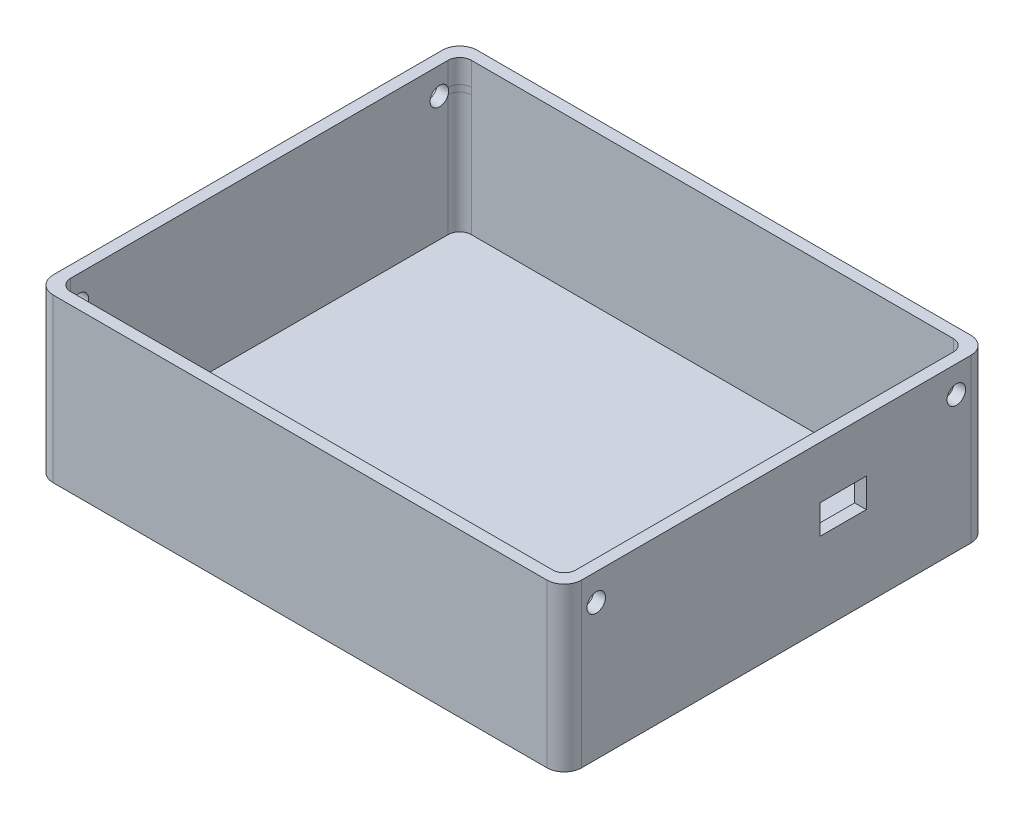
SolidWorks part; units mm, degrees
ref_plane "前视基准面" through (0, 0, 0) normal (0, 0, 1) x (1, 0, 0)
ref_plane "上视基准面" through (0, 0, 0) normal (0, 1, 0) x (1, 0, 0)
ref_plane "右视基准面" through (0, 0, 0) normal (1, 0, 0) x (0, 0, -1)
sketch "草图1" plane through (0, 0, 0) normal (0, 1, 0) x (1, 0, 0)
  line L1 (-45.5, 36.5) -> (45.5, 36.5)
  line L2 (-45.5, 36.5) -> (-45.5, -36.5)
  line L3 (-45.5, -36.5) -> (45.5, -36.5)
  line L4 (45.5, 36.5) -> (45.5, -36.5)
  line L5 (-45.5, 36.5) -> (45.5, -36.5) construction
  line L6 (-45.5, -36.5) -> (45.5, 36.5) construction
  point P0 (0, 0)
  dimension "D1" = 91
  dimension "D2" = 73
extrude "凸台-拉伸1" add sketch "草图1" along normal blind 28
sketch "草图2" plane through (0, 28, 0) normal (0, 1, 0) x (1, 0, 0)
  line L1 (-43.5, 34.5) -> (43.5, 34.5)
  line L2 (-43.5, 34.5) -> (-43.5, -34.5)
  line L3 (-43.5, -34.5) -> (43.5, -34.5)
  line L4 (43.5, 34.5) -> (43.5, -34.5)
  line L5 (-43.5, 34.5) -> (43.5, -34.5) construction
  line L6 (-43.5, -34.5) -> (43.5, 34.5) construction
  point P0 (0, 0)
  dimension "D1" = 87
  dimension "D2" = 69
extrude "切除-拉伸1" cut sketch "草图2" against normal blind 26
sketch "草图3" plane through (43.5, 0, 0) normal (-1, 0, 0) x (0, 0, 1)
  line L0 (-34.5, 28) -> (-7.5, 28) construction
  line L1 (34.5, 28) -> (-34.5, 28) construction
  line L2 (-7.5, 28) -> (-7.5, 19) construction
  line L4 (-7.5, 19) -> (-15.5, 19)
  line L5 (-7.5, 19) -> (-7.5, 14)
  line L6 (-7.5, 14) -> (-15.5, 14)
  line L7 (-15.5, 19) -> (-15.5, 14)
  dimension "D1" = 27
  dimension "D2" = 9
  dimension "D3" = 8
  dimension "D4" = 5
extrude "切除-拉伸2" cut sketch "草图3" against normal blind 26
sketch "草图4" plane through (43.5, 0, 0) normal (-1, 0, 0) x (0, 0, 1)
  line L0 (34.5, 28) -> (27.5, 28) construction
  line L1 (34.5, 28) -> (-34.5, 28) construction
  line L2 (31, 28) -> (31, 23.4) construction
  circle A0 centre (31, 23.4) radius 1.6
  dimension "D1" = 7
  dimension "D2" = 4.6
extrude "切除-拉伸5" cut sketch "草图4" against normal blind 4
mirror "镜向1" about plane through (0, 0, 0) normal (0, 0, 1) of "切除-拉伸5"
mirror "镜向2" about plane through (0, 0, 0) normal (1, 0, 0) of "镜向1", "切除-拉伸5"
fillet "圆角2" radius 3 1 edges at (45.5, 14, 36.5)
fillet "圆角3" radius 3 1 edges at (-45.5, 14, 36.5)
fillet "圆角4" radius 3 1 edges at (-45.5, 14, -36.5)
fillet "圆角5" radius 3 1 edges at (45.5, 14, -36.5)
fillet "圆角6" radius 2 1 edges at (-43.5, 15, -34.5)
fillet "圆角7" radius 2 1 edges at (43.5, 15, -34.5)
fillet "圆角8" radius 2 1 edges at (-43.5, 15, 34.5)
fillet "圆角9" radius 2 1 edges at (43.5, 15, 34.5)
